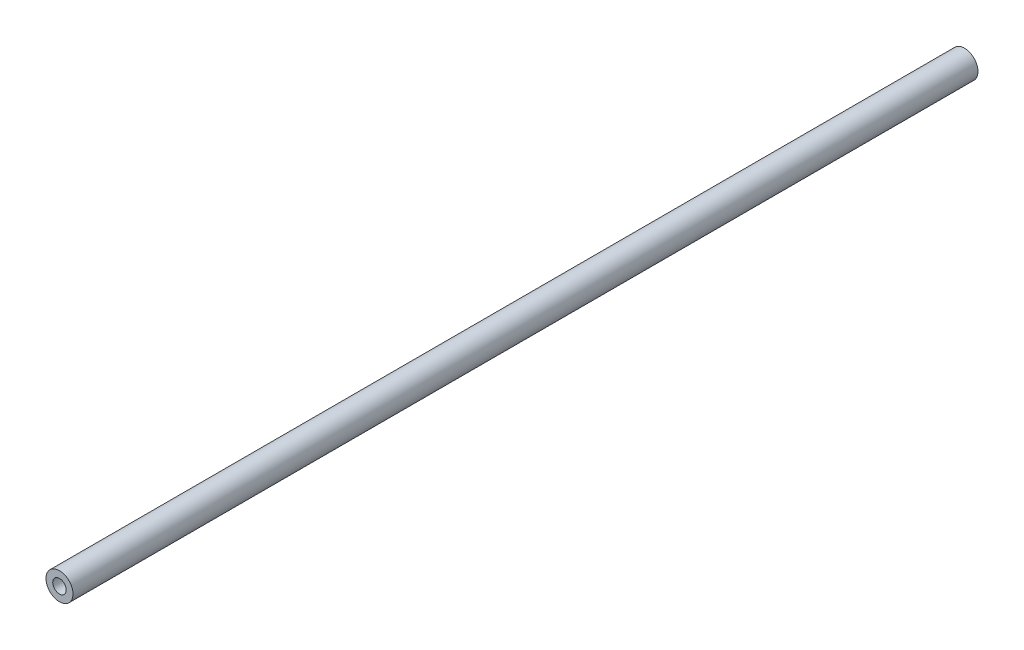
SolidWorks part; units mm, degrees
ref_plane "Ebene vorne" through (0, 0, 0) normal (0, 0, 1) x (1, 0, 0)
ref_plane "Ebene oben" through (0, 0, 0) normal (0, 1, 0) x (1, 0, 0)
ref_plane "Ebene rechts" through (0, 0, 0) normal (1, 0, 0) x (0, 0, -1)
sketch "Skizze1" plane through (0, 0, 0) normal (0, 0, 1) x (1, 0, 0)
  circle A0 centre (0, 0) radius 5
  dimension "D1" = 10
extrude "Aufsatz-Linear austragen1" add sketch "Skizze1" along normal blind 335
sketch "Skizze2" plane through (0, 0, 0) normal (0, 0, 1) x (1, 0, 0)
  circle A0 centre (0, 0) radius 2.5
  dimension "D1" = 5
extrude "Schnitt-Linear austragen3" cut sketch "Skizze2" along normal blind 17
sketch "Skizze3" plane through (0, 0, 335) normal (0, 0, 1) x (1, 0, 0)
  circle A0 centre (0, 0) radius 2.5
  dimension "D1" = 5
extrude "Schnitt-Linear austragen4" cut sketch "Skizze3" against normal blind 17
